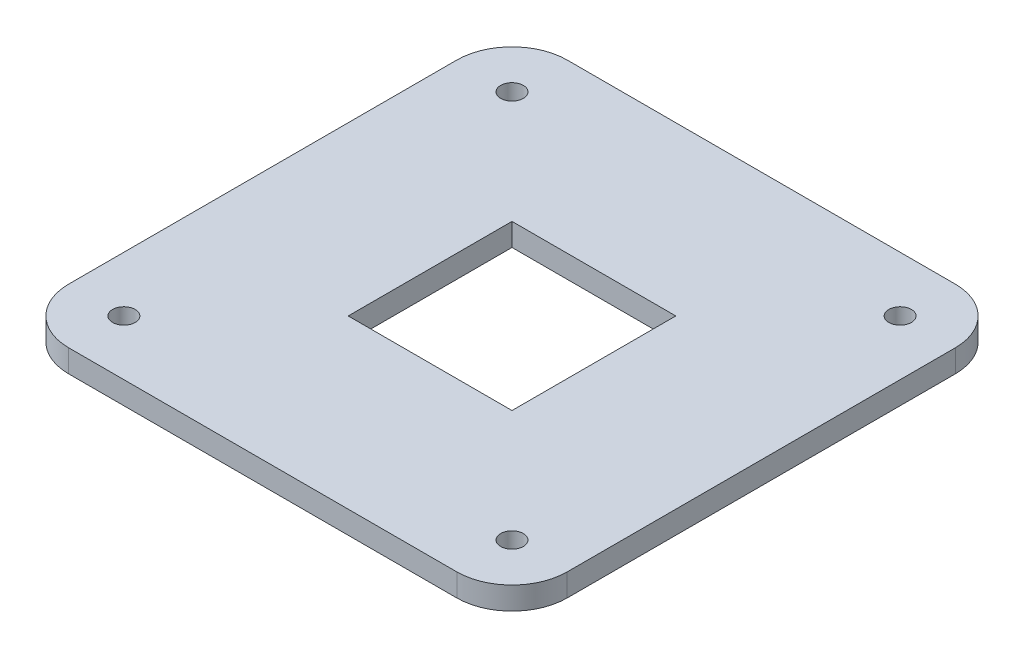
SolidWorks part; units mm, degrees
material "Pino"
ref_plane "Alzado" through (0, 0, 0) normal (0, 0, 1) x (1, 0, 0)
ref_plane "Planta" through (0, 0, 0) normal (0, 1, 0) x (1, 0, 0)
ref_plane "Vista lateral" through (0, 0, 0) normal (1, 0, 0) x (0, 0, -1)
sketch "Croquis1" plane through (0, 0, 0) normal (0, 1, 0) x (1, 0, 0)
  line L1 (-109, 140) -> (109, 140)
  line L2 (-140, 109) -> (-140, -109)
  line L3 (-109, -140) -> (109, -140)
  line L4 (140, 109) -> (140, -109)
  line L5 (-140, 140) -> (140, -140) construction
  line L6 (-140, -140) -> (140, 140) construction
  line L7 (-46, 46) -> (46, 46)
  line L8 (-46, 46) -> (-46, -46)
  line L9 (-46, -46) -> (46, -46)
  line L10 (46, 46) -> (46, -46)
  line L11 (-46, 46) -> (46, -46) construction
  line L12 (-46, -46) -> (46, 46) construction
  arc A0 (-140, -109) -> (-109, -140) centre (-109, -109) ccw
  arc A1 (109, -140) -> (140, -109) centre (109, -109) ccw
  arc A2 (109, 140) -> (140, 109) centre (109, 109) cw
  arc A3 (-109, 140) -> (-140, 109) centre (-109, 109) ccw
  circle A4 centre (-109, -109) radius 6.35
  circle A5 centre (-109, 109) radius 6.35
  circle A6 centre (109, 109) radius 6.35
  circle A7 centre (109, -109) radius 6.35
  point P0 (0, 0)
  point P22 (0, 0)
  dimension "D3" = 31
  dimension "D4" = 12.7
  dimension "D1" = 280
  dimension "D2" = 280
  dimension "D5" = 92
  dimension "D6" = 92
extrude "Saliente-Extruir1" add sketch "Croquis1" along normal blind 12.7
